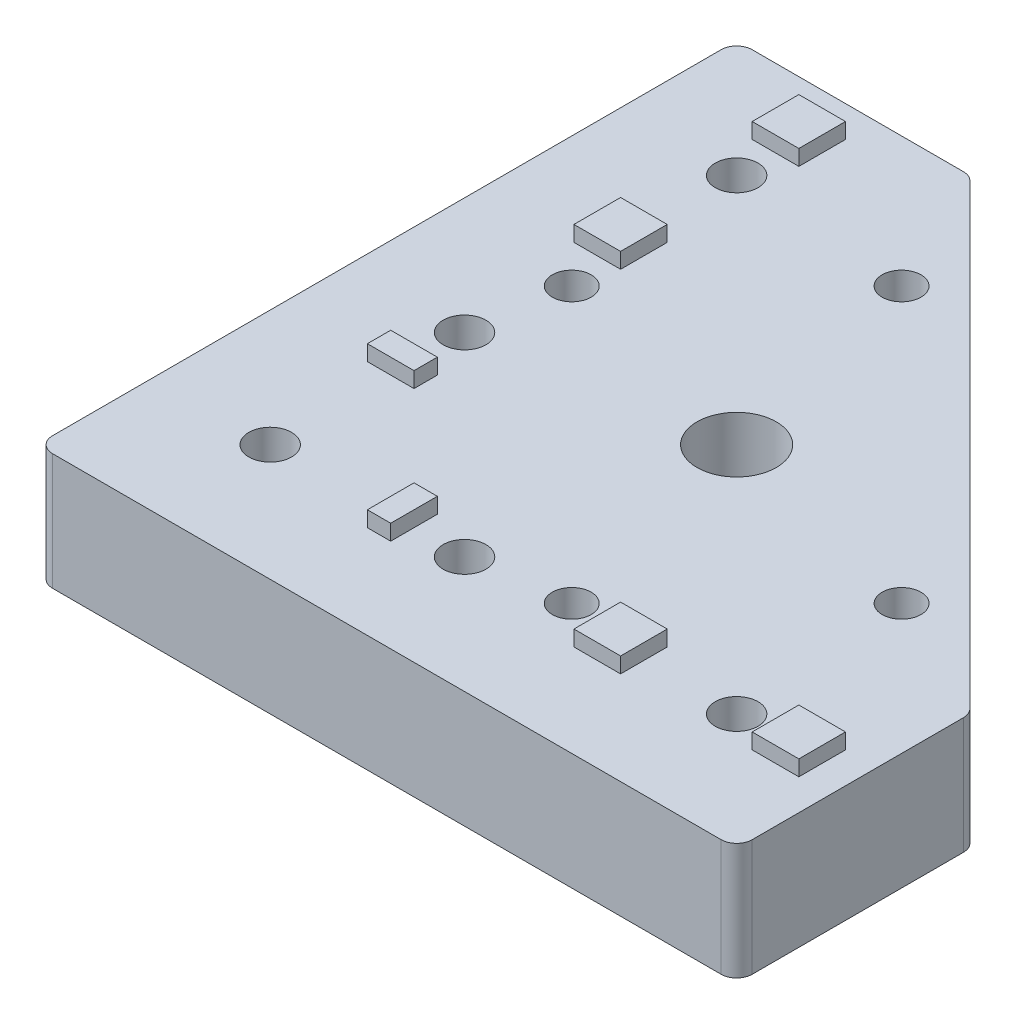
SolidWorks part; units mm, degrees
material "Алюминиевый сплав"
ref_plane "Спереди" through (0, 0, 0) normal (0, 0, 1) x (1, 0, 0)
ref_plane "Сверху" through (0, 0, 0) normal (0, 1, 0) x (1, 0, 0)
ref_plane "Справа" through (0, 0, 0) normal (1, 0, 0) x (0, 0, -1)
sketch "Эскиз1" plane through (0, 0, 0) normal (0, 1, 0) x (1, 0, 0)
  line L0 (0, 0) -> (0, 90)
  line L1 (0, 90) -> (30, 90)
  line L2 (30, 90) -> (90, 30)
  line L3 (90, 30) -> (90, 0)
  line L4 (90, 0) -> (0, 0)
  point P3 (1.2064, 0)
  dimension "D1" = 90
  dimension "D2" = 30
extrude "Бобышка-Вытянуть1" add sketch "Эскиз1" along normal blind 15
hole_wizard "Отверстие обработанное метчиком M121" positions "Эскиз2" profile "Эскиз3" tap size "M12" standard "ISO" end condition up to next
sketch "Эскиз2" plane through (0, 15, 0) normal (0, 1, 0) x (1, 0, 0)
  line L0 (0, 0) -> (90, 0) construction
  line L2 (90, 0) -> (90, 30) construction
  point P0 (45, 45)
  dimension "D1" = 45
  dimension "D2" = 45
sketch "Эскиз3" plane through (45, 15, -45) normal (1, 0, 0) x (0, 0, 1)
  line L0 (0, 0) -> (0, 15)
  line L1 (0, 15) -> (5.1, 15)
  line L2 (5.1, 15) -> (5.1, 0)
  line L5 (5.1, 0) -> (0, 0)
  line L11 (0, -6.35) -> (0, 107.95) construction
  dimension "Диаметр проходного сверла" = 10.2
  dimension "Глубина проходного сверла" = 15
cosmetic thread "Отверстие резьбы1" parameters "D2"=12
hole_wizard "Отверстие обработанное метчиком M61" positions "Эскиз4" profile "Эскиз5" tap size "M6" standard "ISO" end condition up to next
sketch "Эскиз4" plane through (0, 15, 0) normal (0, 1, 0) x (1, 0, 0)
  line L0 (37.9289, 73.2843) -> (16.7157, 52.0711)
  line L1 (16.7157, 52.0711) -> (52.0711, 16.7157)
  line L2 (52.0711, 16.7157) -> (73.2843, 37.9289)
  line L3 (73.2843, 37.9289) -> (37.9289, 73.2843)
  line L5 (90, 30) -> (30, 90) construction
  line L8 (37.9289, 73.2843) -> (52.0711, 16.7157)
  circle A0 centre (45, 45) radius 5.1
  circle A1 centre (45, 45) radius 5.1 construction
  point P0 (37.9289, 73.2843)
  point P2 (73.2843, 37.9289)
  point P4 (52.0711, 16.7157)
  point P6 (16.7157, 52.0711)
  point P41 (0, 0)
  dimension "D1" = 50
  dimension "D2" = 30
sketch "Эскиз5" plane through (37.9289, 15, -73.2843) normal (1, 0, 0) x (0, 0, 1)
  line L0 (0, 0) -> (0, 15)
  line L1 (0, 15) -> (2.5, 15)
  line L2 (2.5, 15) -> (2.5, 0)
  line L5 (2.5, 0) -> (0, 0)
  line L11 (0, -6.35) -> (0, 107.95) construction
  dimension "Диаметр проходного сверла" = 5
  dimension "Глубина проходного сверла" = 15
cosmetic thread "Отверстие резьбы2" parameters "D2"=6
cosmetic thread "Отверстие резьбы3" parameters "D2"=6
cosmetic thread "Отверстие резьбы4" parameters "D2"=6
cosmetic thread "Отверстие резьбы5" parameters "D2"=6
hole_wizard "Диаметр отверстия Ø5.5 (5.5)1" positions "Эскиз6" profile "Эскиз8" hole size "Ø5.5" standard "ISO" end condition up to next
sketch "Эскиз6" plane through (0, 15, 0) normal (0, 1, 0) x (1, 0, 0)
  line L0 (75, 15) -> (40, 15)
  line L1 (40, 15) -> (15, 15)
  line L2 (15, 15) -> (15, 40)
  line L3 (15, 40) -> (15, 75)
  line L5 (0, 0) -> (90, 0) construction
  line L6 (0, 90) -> (0, 0) construction
  point P0 (15, 75)
  point P2 (15, 40)
  point P4 (15, 15)
  point P6 (40, 15)
  point P8 (75, 15)
  dimension "D1" = 15
  dimension "D2" = 15
  dimension "D3" = 25
  dimension "D4" = 35
sketch "Эскиз8" plane through (15, 15, -75) normal (1, 0, 0) x (0, 0, 1)
  line L0 (0, 0) -> (0, 15)
  line L1 (0, 15) -> (2.75, 15)
  line L2 (2.75, 15) -> (2.75, 0)
  line L5 (2.75, 0) -> (0, 0)
  line L11 (0, -6.35) -> (0, 107.95) construction
  dimension "Диаметр сквозного отверстия" = 5.5
  dimension "Глубина сквозного отверстия" = 15
sketch "Эскиз9" plane through (0, 15, 0) normal (0, 1, 0) x (1, 0, 0)
  line L0 (0, 0) -> (60, 60) construction
  line L1 (12, 86) -> (18, 86)
  line L2 (12, 86) -> (12, 80)
  line L3 (12, 80) -> (18, 80)
  line L4 (18, 86) -> (18, 80)
  line L5 (12, 86) -> (18, 80) construction
  line L6 (12, 80) -> (18, 86) construction
  line L7 (12, 63.0711) -> (18, 63.0711)
  line L8 (12, 63.0711) -> (12, 57.0711)
  line L9 (12, 57.0711) -> (18, 57.0711)
  line L10 (18, 63.0711) -> (18, 57.0711)
  line L11 (12, 63.0711) -> (18, 57.0711) construction
  line L12 (12, 57.0711) -> (18, 63.0711) construction
  line L13 (12, 33.5) -> (18, 33.5)
  line L14 (12, 33.5) -> (12, 30.5)
  line L15 (12, 30.5) -> (18, 30.5)
  line L16 (18, 33.5) -> (18, 30.5)
  line L17 (12, 33.5) -> (18, 30.5) construction
  line L18 (12, 30.5) -> (18, 33.5) construction
  line L19 (90, 30) -> (30, 90) construction
  line L20 (15, 83) -> (15, 75) construction
  line L21 (15, 75) -> (15, 60.0711) construction
  line L22 (15, 60.0711) -> (15, 32) construction
  line L23 (60.0711, 15) -> (32, 15) construction
  line L24 (75, 15) -> (60.0711, 15) construction
  line L25 (83, 15) -> (75, 15) construction
  line L26 (30.5, 12) -> (33.5, 18) construction
  line L27 (33.5, 12) -> (30.5, 18) construction
  line L28 (57.0711, 12) -> (63.0711, 18) construction
  line L29 (63.0711, 12) -> (57.0711, 18) construction
  line L30 (80, 12) -> (86, 18) construction
  line L31 (86, 12) -> (80, 18) construction
  line L32 (33.5, 18) -> (30.5, 18)
  line L33 (30.5, 12) -> (30.5, 18)
  line L34 (33.5, 12) -> (30.5, 12)
  line L35 (33.5, 12) -> (33.5, 18)
  line L36 (63.0711, 18) -> (57.0711, 18)
  line L37 (57.0711, 12) -> (57.0711, 18)
  line L38 (63.0711, 12) -> (57.0711, 12)
  line L39 (63.0711, 12) -> (63.0711, 18)
  line L40 (86, 18) -> (80, 18)
  line L41 (80, 12) -> (80, 18)
  line L42 (86, 12) -> (80, 12)
  line L43 (86, 12) -> (86, 18)
  circle A0 centre (15, 75) radius 2.75 construction
  circle A1 centre (15, 40) radius 2.75 construction
  circle A2 centre (16.7157, 52.0711) radius 2.5 construction
  point P0 (15, 83)
  point P5 (15, 60.0711)
  point P10 (15, 32)
  point P23 (12, 80.1439)
  point P26 (12, 65.5613)
  point P31 (18, 33.6701)
  point P32 (18, 30.3688)
  point P51 (32, 15)
  point P52 (60.0711, 15)
  point P53 (83, 15)
  dimension "D5" = 8
  dimension "D1" = 6
  dimension "D2" = 8
  dimension "D3" = 8
  dimension "D4" = 3
extrude "Бобышка-Вытянуть2" add sketch "Эскиз9" along normal blind 2
fillet "Скругление1" radius 2 5 edges at (0, 7.5, -90) (0, 7.5, 0) (90, 7.5, 0) (90, 7.5, -30) (30, 7.5, -90)
